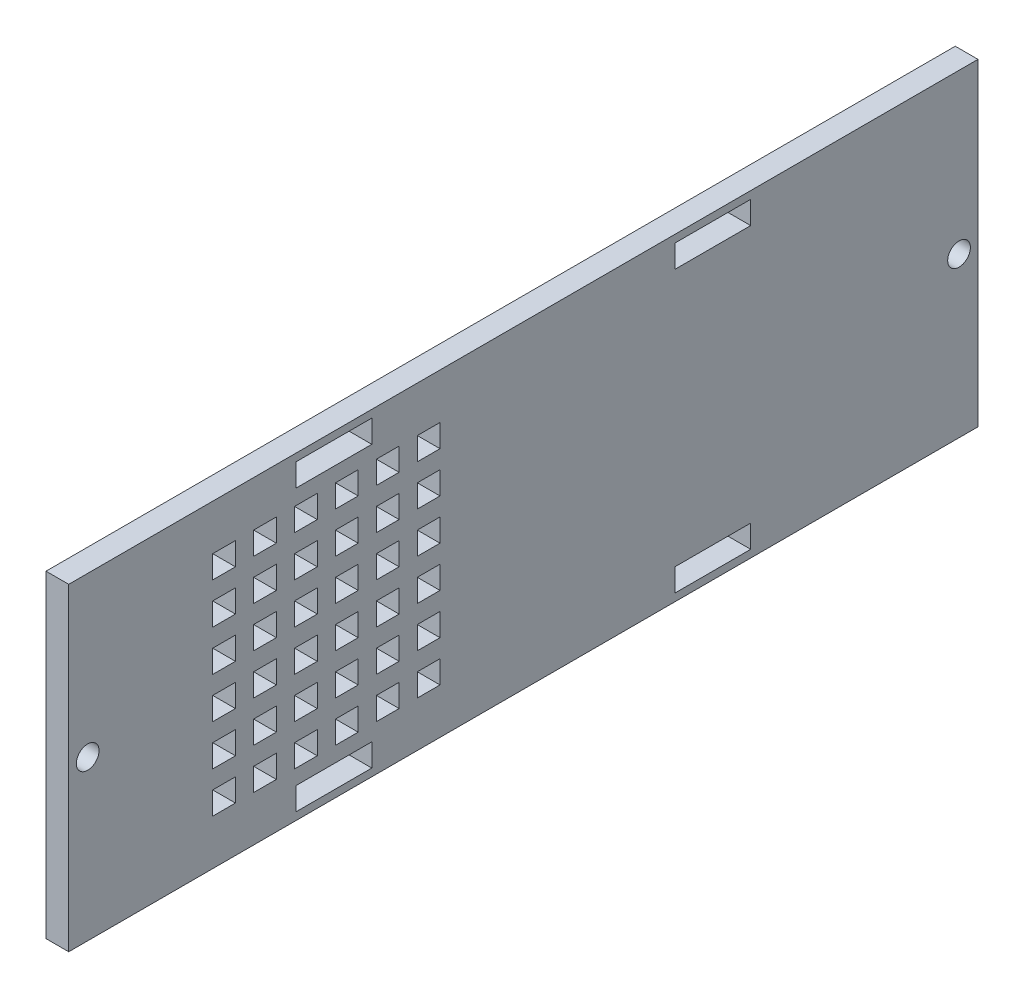
SolidWorks part; units mm, degrees
ref_plane "Front Plane" through (0, 0, 0) normal (0, 0, 1) x (1, 0, 0)
ref_plane "Top Plane" through (0, 0, 0) normal (0, 1, 0) x (1, 0, 0)
ref_plane "Right Plane" through (0, 0, 0) normal (1, 0, 0) x (0, 0, -1)
sketch "Sketch1" plane through (0, 0, 0) normal (1, 0, 0) x (0, 0, -1)
  line L0 (30, 17) -> (20, 17)
  line L1 (-20, 17) -> (-30, 17)
  line L2 (-30, -17) -> (-20, -17)
  line L3 (20, -17) -> (30, -17)
  line L14 (30, 20) -> (20, 20)
  line L15 (30, 20) -> (30, 17)
  line L17 (20, 20) -> (20, 17)
  line L18 (30, 20) -> (20, 17) construction
  line L22 (0, 0) -> (0, 41.0344) construction
  line L25 (30, 17) -> (20, 20) construction
  line L26 (30, -17) -> (30, -20)
  line L27 (30, -20) -> (20, -20)
  line L28 (20, -17) -> (20, -20)
  line L29 (30, -17) -> (20, -20) construction
  line L30 (30, -20) -> (20, -17) construction
  line L32 (-20, 20) -> (-30, 20)
  line L33 (-20, 20) -> (-20, 17)
  line L35 (-30, 20) -> (-30, 17)
  line L36 (-20, 20) -> (-30, 17) construction
  line L37 (-20, 17) -> (-30, 20) construction
  line L38 (-20, -17) -> (-20, -20)
  line L39 (-20, -20) -> (-30, -20)
  line L40 (-30, -17) -> (-30, -20)
  line L41 (-20, -17) -> (-30, -20) construction
  line L42 (-20, -20) -> (-30, -17) construction
  line L43 (0, 0) -> (0, -51.197) construction
  line L45 (60, -21) -> (-60, -21)
  line L46 (60, -21) -> (60, 21)
  line L47 (60, 21) -> (-60, 21)
  line L48 (-60, -21) -> (-60, 21)
  line L49 (60, -21) -> (-60, 21) construction
  line L50 (60, 21) -> (-60, -21) construction
  circle A0 centre (-57.5, 0) radius 1.5 construction
  circle A1 centre (57.5, 0) radius 1.5 construction
  circle A2 centre (-57.5, 0) radius 1.5
  circle A3 centre (57.5, 0) radius 1.5
  point P0 (0, 0)
  point P1 (0, 0)
  point P2 (60, 0)
  point P3 (0, 21)
  point P15 (25, 18.5)
  point P25 (25, -18.5)
  point P32 (-25, 18.5)
  point P37 (-25, -18.5)
  dimension "D19" = 42
  dimension "D3" = 2.5
  dimension "D4" = 2.5
  dimension "D5" = 3
  dimension "D6" = 10
  dimension "D7" = 2.5
  dimension "D8" = 2.5
  dimension "D9" = 3
  dimension "D10" = 10
  dimension "D11" = 3
  dimension "D12" = 10
  dimension "D13" = 3
  dimension "D14" = 10
  dimension "D15" = 20
  dimension "D16" = 20
  dimension "D17" = 20
  dimension "D18" = 20
  dimension "D20" = 120
extrude "Boss-Extrude1" add sketch "Sketch1" along normal blind 3
sketch "Sketch2" plane through (3, 0, 0) normal (1, 0, 0) x (0, 0, -1)
  line L0 (-60, 21) -> (-60, -21) construction
  line L1 (-14, 12) -> (-11, 12)
  line L2 (-14, 12) -> (-14, 15)
  line L3 (-14, 15) -> (-11, 15)
  line L4 (-11, 12) -> (-11, 15)
  line L5 (-14, 12) -> (-11, 15) construction
  line L6 (-14, 15) -> (-11, 12) construction
  line L7 (60, 21) -> (-60, 21) construction
  point P4 (-12.5, 13.5)
  point P5 (0, 0)
  dimension "D1" = 3
  dimension "D2" = 47.5
  dimension "D3" = 7.5
extrude "Cut-Extrude1" cut sketch "Sketch2" against normal up to next (3 mm away)
pattern_linear "LPattern1" count 6 spacing 5.4 along (0, 0, 1) count 6 spacing 5.4 along (0, -1, 0) of "Cut-Extrude1"
